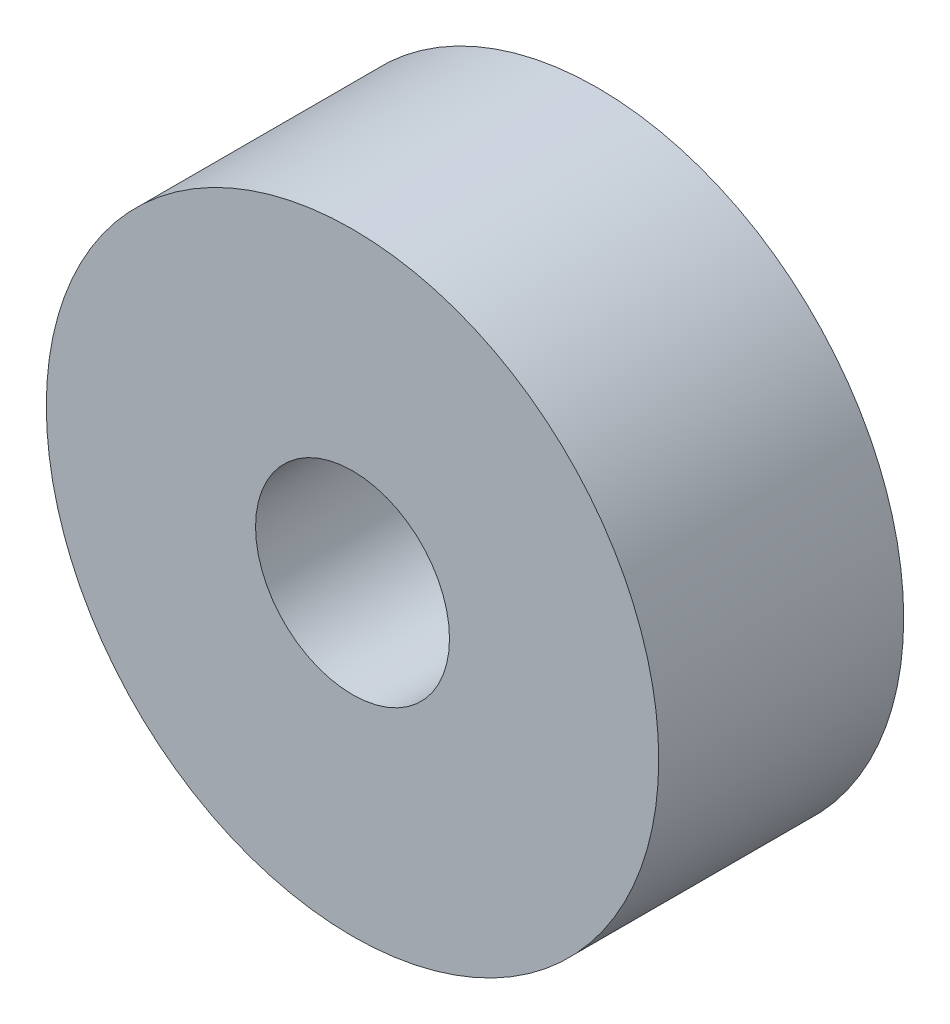
SolidWorks part; units mm, degrees
ref_plane "Front Plane" through (0, 0, 0) normal (0, 0, 1) x (1, 0, 0)
ref_plane "Top Plane" through (0, 0, 0) normal (0, 1, 0) x (1, 0, 0)
ref_plane "Right Plane" through (0, 0, 0) normal (1, 0, 0) x (0, 0, -1)
sketch "Sketch1" plane through (0, 0, 0) normal (0, 0, 1) x (1, 0, 0)
  circle A0 centre (0, 0) radius 4.75
  circle A1 centre (0, 0) radius 15
extrude "Boss-Extrude1" add sketch "Sketch1" along normal blind 12
